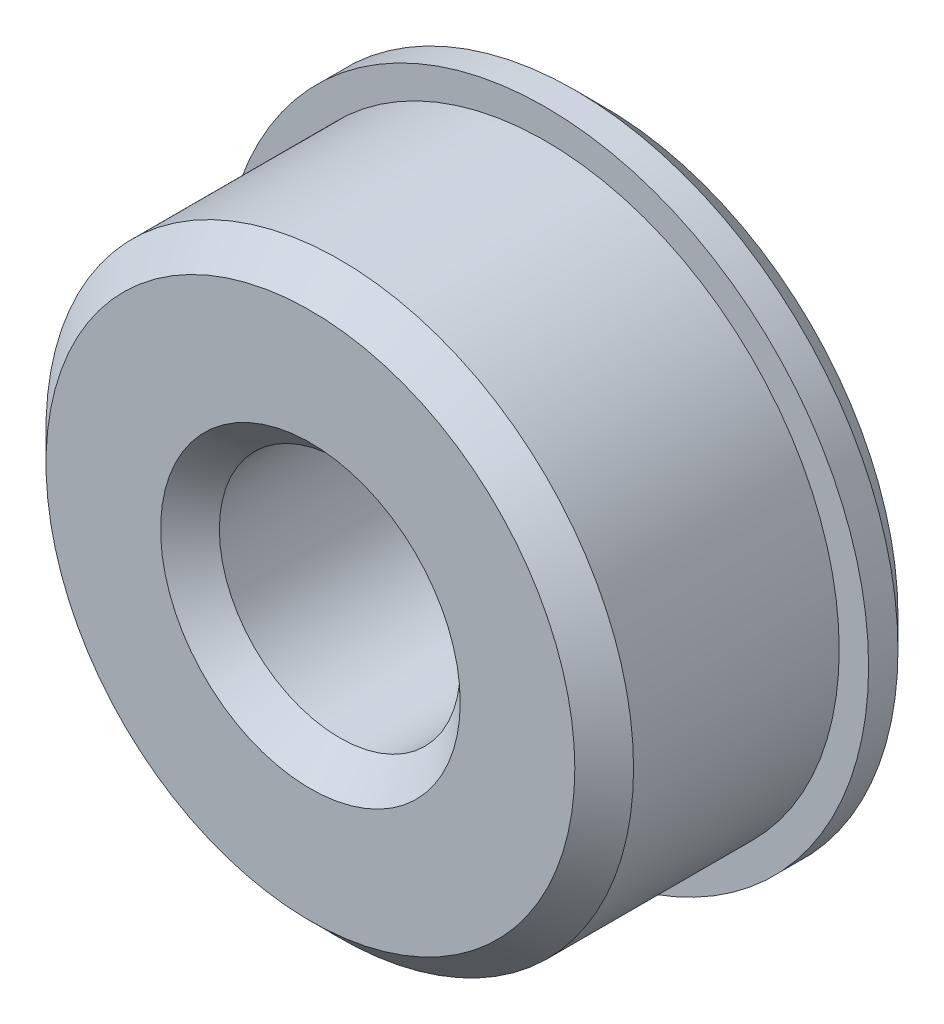
SolidWorks part; units mm, degrees
ref_plane "Front Plane" through (0, 0, 0) normal (0, 0, 1) x (1, 0, 0)
ref_plane "Top Plane" through (0, 0, 0) normal (0, 1, 0) x (1, 0, 0)
ref_plane "Right Plane" through (0, 0, 0) normal (1, 0, 0) x (0, 0, -1)
sketch "Sketch1" plane through (0, 0, 0) normal (0, 0, 1) x (1, 0, 0)
  circle A0 centre (0, 0) radius 5
  dimension "D2" = 10
extrude "Boss-Extrude1" add sketch "Sketch1" along normal blind 4
sketch "Sketch2" plane through (0, 0, 0) normal (0, 0, 1) x (1, 0, 0)
  circle A0 centre (0, 0) radius 5.5
  dimension "D1" = 11
extrude "Boss-Extrude2" add sketch "Sketch2" against normal blind 1
sketch "Sketch3" plane through (0, 0, 4) normal (0, 0, 1) x (1, 0, 0)
  circle A0 centre (0, 0) radius 2.05
  dimension "D1" = 4.1
extrude "Cut-Extrude1" cut sketch "Sketch3" against normal through all
chamfer "Chamfer1" distance 0.5 angle 45 4 edges at (5.5, 0, -1) (2.05, 0, -1) (5, 0, 4) (2.05, 0, 4)
equation "\"q\"=6"
